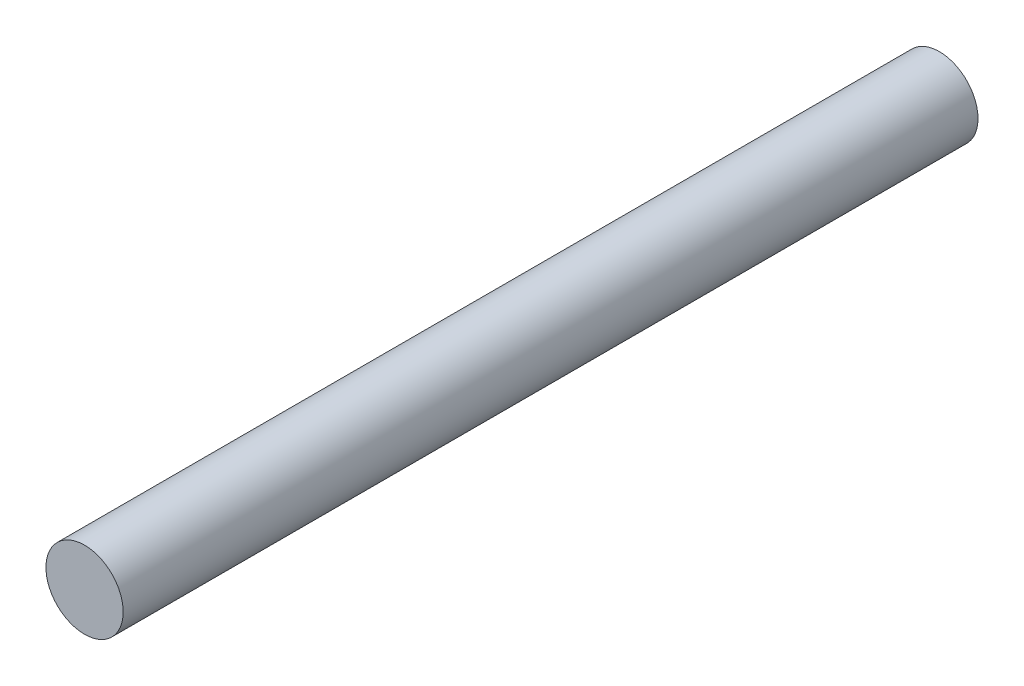
SolidWorks part; units mm, degrees
ref_plane "Front Plane" through (0, 0, 0) normal (0, 0, 1) x (1, 0, 0)
ref_plane "Top Plane" through (0, 0, 0) normal (0, 1, 0) x (1, 0, 0)
ref_plane "Right Plane" through (0, 0, 0) normal (1, 0, 0) x (0, 0, -1)
sketch "Sketch1" plane through (0, 0, 0) normal (0, 0, 1) x (1, 0, 0)
  circle A0 centre (0, 0) radius 1.2065
extrude "Extrude1" add sketch "Sketch1" along normal blind 26.6954
sketch "Sketch2" plane through (0, 0, 0) normal (0, 0, -1) x (-1, 0, 0)
  line L0 (0, 0) -> (0, 1.2065)
  circle A0 centre (0, 0) radius 1.2065 construction
